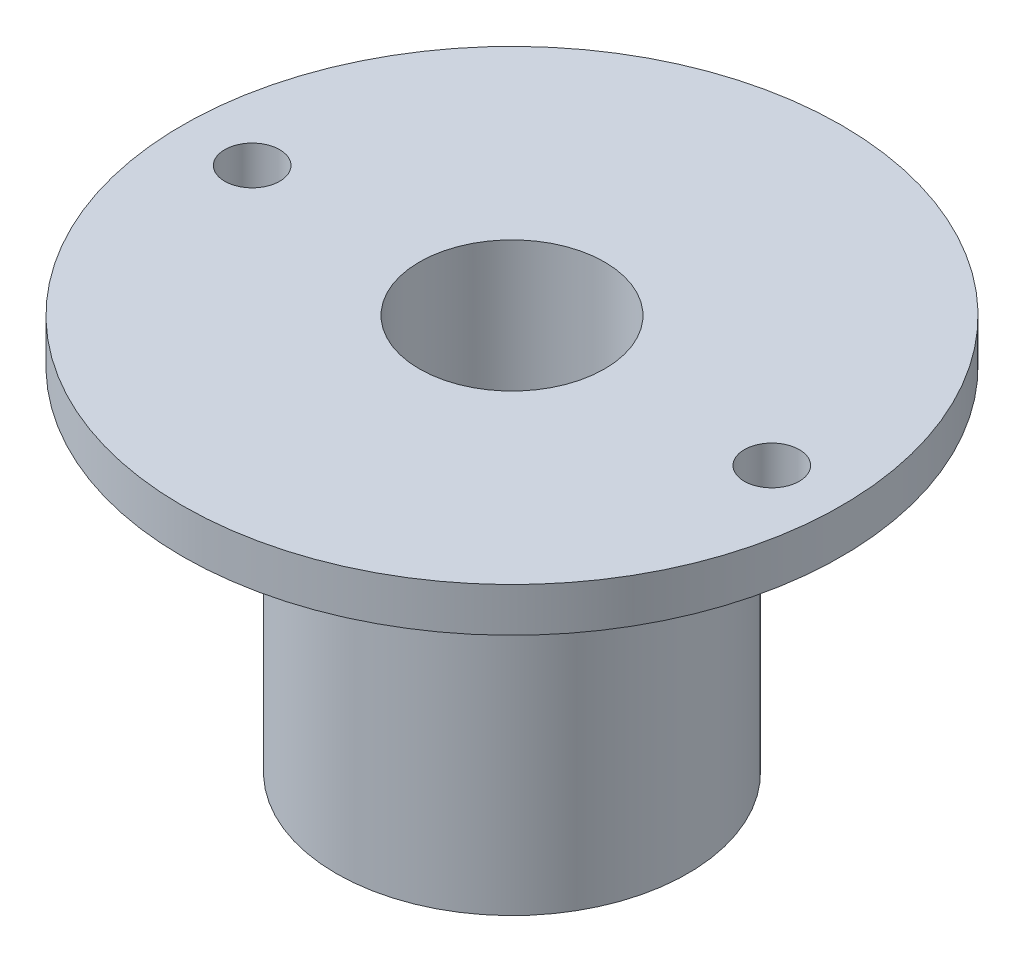
SolidWorks part; units mm, degrees
ref_plane "Front Plane" through (0, 0, 0) normal (0, 0, 1) x (1, 0, 0)
ref_plane "Top Plane" through (0, 0, 0) normal (0, 1, 0) x (1, 0, 0)
ref_plane "Right Plane" through (0, 0, 0) normal (1, 0, 0) x (0, 0, -1)
sketch "Sketch1" plane through (0, 0, 0) normal (0, 1, 0) x (1, 0, 0)
  circle A0 centre (0, 0) radius 15
  dimension "D1" = 30
extrude "Boss-Extrude1" add sketch "Sketch1" against normal blind 2
sketch "Sketch2" plane through (0, -2, 0) normal (0, -1, 0) x (1, 0, 0)
  circle A0 centre (0, 0) radius 8
  dimension "D1" = 16
extrude "Boss-Extrude2" add sketch "Sketch2" along normal blind 16
hole_wizard "3/8-24 Tapped Hole1" positions "Sketch4" profile "Sketch3" tap size "3/8-24" standard "ANSI Inch"
sketch "Sketch4" plane through (0, -18, 0) normal (0, -1, 0) x (-1, 0, 0)
  point P0 (0, 0)
sketch "Sketch3" plane through (0, -18, 0) normal (1, 0, 0) x (0, 0, -1)
  line L0 (0, 0) -> (0, 26.9335)
  line L1 (0, 26.9335) -> (4.2164, 24.4)
  line L2 (4.2164, 24.4) -> (4.2164, 0)
  line L5 (4.2164, 0) -> (0, 0)
  line L10 (0, 26.9335) -> (-4.2164, 24.4) construction
  line L11 (0, -6.35) -> (0, 107.95) construction
  dimension "Tap Drill Dia." = 8.4328
  dimension "Tap Drill Depth" = 24.4
  dimension "Drill Angle" = 118
cosmetic thread "Hole Thread1" parameters "D1"=18, "D2"=9.525
sketch "Sketch5" plane through (0, 0, 0) normal (0, 1, 0) x (1, 0, 0)
  line L0 (11.825, 0) -> (-11.825, 0) construction
  circle A0 centre (11.825, 0) radius 1.25
  circle A1 centre (-11.825, 0) radius 1.25
  point P9 (0, 0)
  dimension "D2" = 2.5
  dimension "D1" = 23.65
extrude "Cut-Extrude1" cut sketch "Sketch5" against normal blind 10
